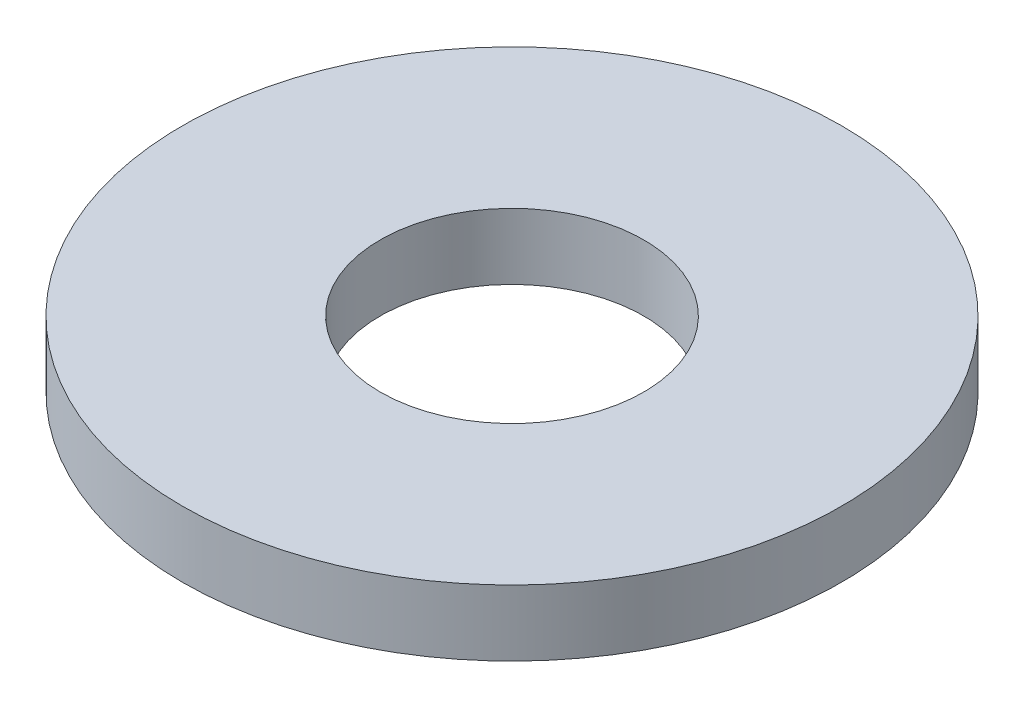
SolidWorks part; units mm, degrees
material "Brass"
ref_plane "Front Plane" through (0, 0, 0) normal (0, 0, 1) x (1, 0, 0)
ref_plane "Top Plane" through (0, 0, 0) normal (0, 1, 0) x (1, 0, 0)
ref_plane "Right Plane" through (0, 0, 0) normal (1, 0, 0) x (0, 0, -1)
sketch "Sketch1" plane through (0, 0, 0) normal (0, 1, 0) x (1, 0, 0)
  circle A0 centre (0, 0) radius 7.9375
  circle A1 centre (0, 0) radius 3.175
  dimension "D1" = 6.35
  dimension "D2" = 15.875
extrude "Boss-Extrude1" add sketch "Sketch1" along normal blind 1.5875
